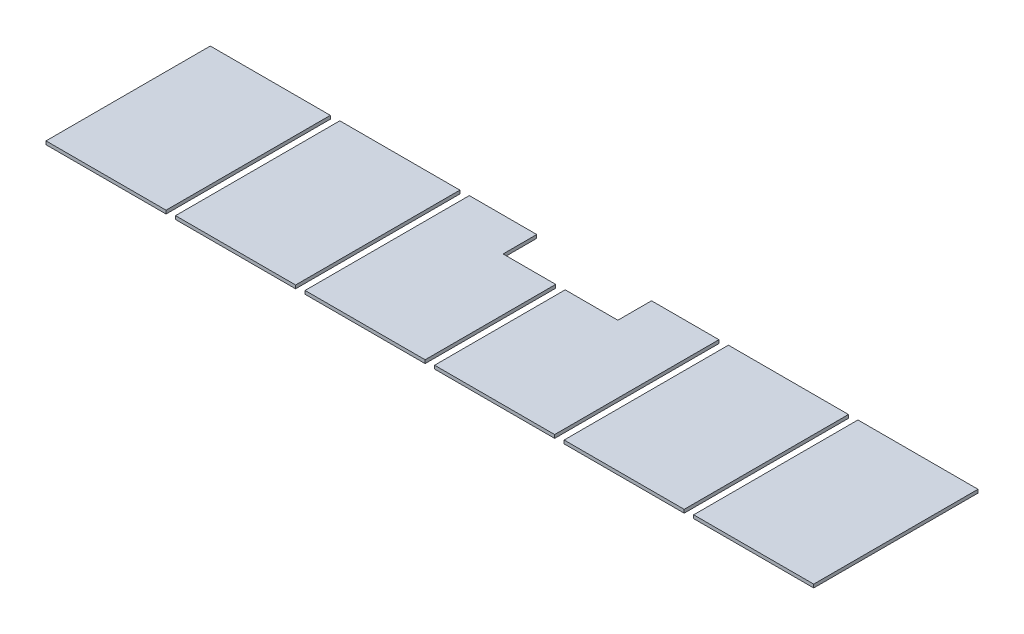
SolidWorks part; units mm, degrees
ref_plane "Front Plane" through (0, 0, 0) normal (0, 0, 1) x (1, 0, 0)
ref_plane "Top Plane" through (0, 0, 0) normal (0, 1, 0) x (1, 0, 0)
ref_plane "Right Plane" through (0, 0, 0) normal (1, 0, 0) x (0, 0, -1)
sketch "Sketch2" plane through (0, 0, 0) normal (0, 1, 0) x (1, 0, 0)
  line L4 (3073.4, 2044.7) -> (1625.6, 2044.7)
  line L5 (1625.6, 2044.7) -> (1625.6, 63.5)
  line L6 (1625.6, 63.5) -> (3073.4, 63.5)
  line L7 (3073.4, 63.5) -> (3073.4, 2044.7)
  line L8 (3073.4, 2044.7) -> (1625.6, 2044.7)
  line L9 (1625.6, 2044.7) -> (1625.6, 63.5)
  line L10 (1625.6, 63.5) -> (3073.4, 63.5)
  line L11 (3073.4, 63.5) -> (3073.4, 2044.7)
  line L12 (1511.3, 2044.7) -> (63.5, 2044.7)
  line L13 (63.5, 2044.7) -> (63.5, 63.5)
  line L14 (63.5, 63.5) -> (1511.3, 63.5)
  line L15 (1511.3, 63.5) -> (1511.3, 2044.7)
  line L16 (1511.3, 2044.7) -> (63.5, 2044.7)
  line L17 (63.5, 2044.7) -> (63.5, 63.5)
  line L18 (63.5, 63.5) -> (1511.3, 63.5)
  line L19 (1511.3, 63.5) -> (1511.3, 2044.7)
  line L20 (9321.8, 2044.7) -> (7874, 2044.7)
  line L21 (7874, 2044.7) -> (7874, 63.5)
  line L22 (7874, 63.5) -> (9321.8, 63.5)
  line L23 (9321.8, 63.5) -> (9321.8, 2044.7)
  line L24 (9321.8, 2044.7) -> (7874, 2044.7)
  line L25 (7874, 2044.7) -> (7874, 63.5)
  line L26 (7874, 63.5) -> (9321.8, 63.5)
  line L27 (9321.8, 63.5) -> (9321.8, 2044.7)
  line L28 (7759.7, 63.5) -> (7759.7, 2044.7)
  line L29 (6311.9, 63.5) -> (7759.7, 63.5)
  line L30 (6311.9, 2044.7) -> (6311.9, 63.5)
  line L31 (7759.7, 2044.7) -> (6311.9, 2044.7)
  line L32 (7759.7, 63.5) -> (7759.7, 2044.7)
  line L33 (6311.9, 63.5) -> (7759.7, 63.5)
  line L34 (6311.9, 2044.7) -> (6311.9, 63.5)
  line L35 (7759.7, 2044.7) -> (6311.9, 2044.7)
  line L36 (11976.1, 2298.7) -> (9436.1, 2298.7)
  line L37 (11976.1, 50.8) -> (11976.1, 2298.7)
  line L38 (6197.6, 2044.7) -> (5384.8, 2044.7)
  line L39 (6197.6, 63.5) -> (6197.6, 2044.7)
  line L40 (4749.8, 63.5) -> (6197.6, 63.5)
  line L41 (4749.8, 1638.3) -> (4749.8, 63.5)
  line L42 (5384.8, 1638.3) -> (4749.8, 1638.3)
  line L43 (5384.8, 2044.7) -> (5384.8, 1638.3)
  line L44 (6197.6, 2044.7) -> (5384.8, 2044.7)
  line L45 (6197.6, 63.5) -> (6197.6, 2044.7)
  line L46 (4749.8, 63.5) -> (6197.6, 63.5)
  line L47 (4749.8, 1638.3) -> (4749.8, 63.5)
  line L48 (5384.8, 1638.3) -> (4749.8, 1638.3)
  line L49 (5384.8, 2044.7) -> (5384.8, 1638.3)
  line L50 (3187.7, 2044.7) -> (3187.7, 63.5)
  line L51 (4000.5, 2044.7) -> (3187.7, 2044.7)
  line L52 (4000.5, 1638.3) -> (4000.5, 2044.7)
  line L53 (4635.5, 1638.3) -> (4000.5, 1638.3)
  line L54 (4635.5, 63.5) -> (4635.5, 1638.3)
  line L55 (3187.7, 63.5) -> (4635.5, 63.5)
  line L56 (3187.7, 2044.7) -> (3187.7, 63.5)
  line L57 (4000.5, 2044.7) -> (3187.7, 2044.7)
  line L58 (4000.5, 1638.3) -> (4000.5, 2044.7)
  line L59 (4635.5, 1638.3) -> (4000.5, 1638.3)
  line L60 (4635.5, 63.5) -> (4635.5, 1638.3)
  line L61 (3187.7, 63.5) -> (4635.5, 63.5)
  line L62 (9436.1, 50.8) -> (11976.1, 50.8)
  line L63 (9436.1, 2298.7) -> (9436.1, 50.8)
  line L64 (11976.1, 2298.7) -> (9436.1, 2298.7)
  line L65 (11976.1, 50.8) -> (11976.1, 2298.7)
  line L66 (9436.1, 50.8) -> (11976.1, 50.8)
  line L67 (9436.1, 2298.7) -> (9436.1, 50.8)
  dimension "D1" = 0
  dimension "D2" = 0
  dimension "D3" = 0
  dimension "D4" = 0
  dimension "D5" = 0
  dimension "D6" = 0
  dimension "D7" = 0
extrude "Boss-Extrude1" add sketch "Sketch2" along normal up to surface (40.64 mm away) contours L18 L19 L16 L17 | L10 L11 L8 L9 | L56 L61 L60 L59 L58 L57 | L44 L49 L48 L47 L46 L45 | L32 L35 L34 L33 | L26 L27 L24 L25
